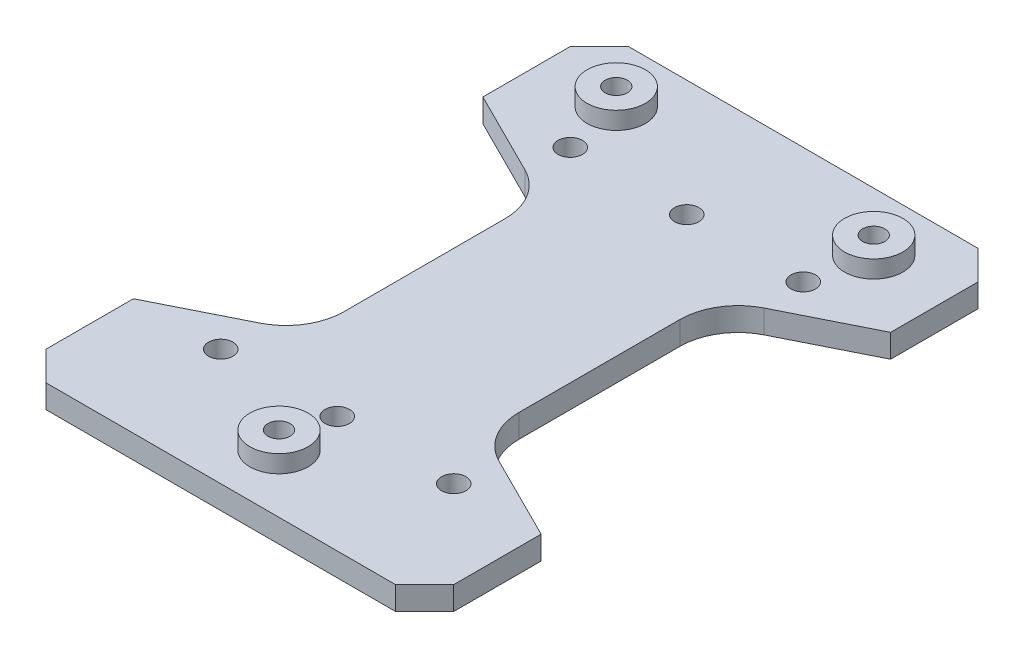
SolidWorks part; units mm, degrees
ref_plane "Front Plane" through (0, 0, 0) normal (0, 0, 1) x (1, 0, 0)
ref_plane "Top Plane" through (0, 0, 0) normal (0, 1, 0) x (1, 0, 0)
ref_plane "Right Plane" through (0, 0, 0) normal (1, 0, 0) x (0, 0, -1)
sketch "草圖1" plane through (0, 0, 0) normal (0, 1, 0) x (1, 0, 0)
  line L1 (-35, 50) -> (35, 50)
  line L2 (-35, 50) -> (-35, -50)
  line L3 (-35, -50) -> (35, -50)
  line L4 (35, 50) -> (35, -50)
  line L5 (-35, 50) -> (35, -50) construction
  line L6 (-35, -50) -> (35, 50) construction
  point P0 (0, 0)
  dimension "D1" = 70
  dimension "D2" = 100
extrude "填料-伸長1" add sketch "草圖1" along normal blind 4
sketch "草圖2" plane through (0, 4, 0) normal (0, 1, 0) x (1, 0, 0)
  line L0 (0, 40) -> (0, -40) construction
  line L1 (0, -40) -> (0, -50) construction
  line L2 (-35, -50) -> (35, -50) construction
  line L3 (-22.1, 40) -> (22.1, 40) construction
  circle A0 centre (-22.1, 40) radius 5
  circle A1 centre (22.1, 40) radius 5
  circle A2 centre (0, -40) radius 5
  point P8 (0, 40)
  dimension "D4" = 10
  dimension "D1" = 80
  dimension "D2" = 10
  dimension "D3" = 44.2
extrude "填料-伸長2" add sketch "草圖2" along normal blind 3
sketch "草圖3" plane through (0, 7, 0) normal (0, 1, 0) x (1, 0, 0)
  circle A0 centre (-22.1, 40) radius 1.9
  circle A1 centre (22.1, 40) radius 1.9
  circle A2 centre (0, -40) radius 1.9
  dimension "D1" = 3.8
extrude "除料-伸長1" cut sketch "草圖3" against normal blind 4
sketch "草圖6" plane through (0, 4, 0) normal (0, 1, 0) x (1, 0, 0)
  line L0 (0, 50) -> (0, 30) construction
  line L1 (35, 50) -> (-35, 50) construction
  line L2 (0, 30) -> (-20, 30) construction
  circle A0 centre (-20, 30) radius 2.1
  dimension "D3" = 4.2
  dimension "D1" = 20
  dimension "D2" = 20
extrude "除料-伸長4" cut sketch "草圖6" against normal through all
pattern_linear "直線複製排列1" count 3 spacing 20 along (1, 0, 0) count 4 spacing 20 along (0, 0, 1) skipping (0, 1), (0, 2), (1, 1), (1, 2), (2, 1), (2, 2) of "除料-伸長4"
sketch "草圖7" plane through (0, 4, 0) normal (0, 1, 0) x (1, 0, 0)
  line L0 (-35, 30) -> (-15, 20)
  line L1 (-35, 50) -> (-35, -50) construction
  line L2 (-15, 20) -> (-15, -20)
  line L3 (-15, -20) -> (-35, -30)
  line L4 (-35, -30) -> (-35, 30)
  line L5 (0, 0) -> (-15, 0) construction
  dimension "D1" = 40
  dimension "D2" = 60
  dimension "D3" = 20
extrude "除料-伸長5" cut sketch "草圖7" against normal through all and the other way through all
mirror "鏡射1" about plane through (0, 0, 0) normal (1, 0, 0) of "除料-伸長5"
chamfer "導角1" distance 5 angle 45 4 edges at (35, 2, -50) (-35, 2, -50) (35, 2, 50) (-35, 2, 50)
fillet "圓角1" radius 10 4 edges at (15, 2, -20) (15, 2, 20) (-15, 2, 20) (-15, 2, -20)
